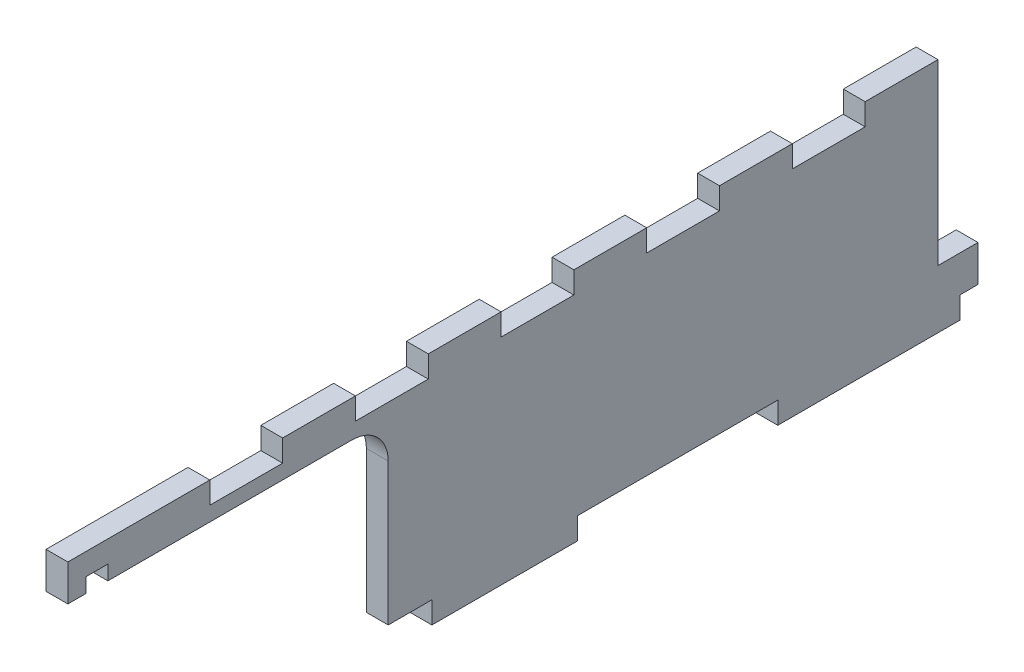
SolidWorks part; units mm, degrees
ref_plane "Front Plane" through (0, 0, 0) normal (0, 0, 1) x (1, 0, 0)
ref_plane "Top Plane" through (0, 0, 0) normal (0, 1, 0) x (1, 0, 0)
ref_plane "Right Plane" through (0, 0, 0) normal (1, 0, 0) x (0, 0, -1)
sketch "Sketch1" plane through (0, 0, 0) normal (1, 0, 0) x (0, 0, -1)
  line L0 (0, 0) -> (250, 0)
  line L1 (250, 0) -> (250, 65)
  line L2 (0, 65) -> (60, 65)
  line L3 (0, 65) -> (0, 0)
  line L4 (60, 65) -> (250, 65)
  point P3 (244, 65)
  point P7 (60, 65)
  point P8 (0, 0)
  point P9 (0, 73.221)
  point P10 (0, 65)
  point P11 (0, 65)
  point P12 (250, 30)
  dimension "D1" = 250
  dimension "D3" = 6
  dimension "D5" = 65
  dimension "D2" = 65
  dimension "D4" = 60
extrude "Boss-Extrude1" add sketch "Sketch1" along normal mid plane 6
sketch "Sketch3" plane through (3, 0, 0) normal (1, 0, 0) x (0, 0, -1)
  line L1 (0, 0) -> (88, 0)
  line L2 (0, 0) -> (0, 55)
  line L3 (0, 55) -> (78, 55)
  line L4 (88, 0) -> (88, 45)
  arc A0 (78, 55) -> (88, 45) centre (78, 45) cw
  dimension "D3" = 10
  dimension "D1" = 88
  dimension "D2" = 55
extrude "Cut-Extrude1" cut sketch "Sketch3" against normal up to surface (6 mm away) up to face at (-3, 32.5, -125)
sketch "Sketch4" plane through (3, 0, 0) normal (1, 0, 0) x (0, 0, -1)
  line L0 (88, 0) -> (250, 0) construction
  line L1 (245, 0) -> (195, 0)
  line L2 (245, 0) -> (245, 6)
  line L3 (250, 65) -> (0, 65) construction
  line L4 (195, 0) -> (195, 6)
  line L5 (250, 0) -> (250, 65) construction
  line L6 (140, 0) -> (100, 0)
  line L7 (140, 0) -> (140, 6)
  line L8 (245, 16) -> (239, 16)
  line L9 (100, 0) -> (100, 6)
  line L10 (140, 6) -> (195, 6)
  line L11 (100, 6) -> (88, 6)
  line L12 (88, 0) -> (88, 45) construction
  line L13 (245, 6) -> (250, 6)
  line L14 (239, 65) -> (250, 65)
  line L15 (78, 55) -> (0, 55) construction
  line L16 (239, 16) -> (239, 65)
  line L17 (245, 16) -> (250, 16)
  line L18 (5, 55) -> (11, 55)
  line L19 (5, 55) -> (5, 59)
  line L20 (250, 16) -> (250, 65)
  line L21 (5, 59) -> (11, 59)
  line L22 (11, 55) -> (11, 59)
  line L23 (250, 65) -> (0, 65) construction
  line M5 (0, 55) -> (78, 55)
  line M7 (88, 45) -> (88, 0)
  line M8 (88, 0) -> (250, 0)
  line M9 (250, 0) -> (250, 65)
  line M10 (250, 65) -> (0, 65)
  dimension "D1" = 6
  dimension "D2" = 5
  dimension "D3" = 50
  dimension "D4" = 55
  dimension "D5" = 40
  dimension "D6" = 6
  dimension "D7" = 10
  dimension "D8" = 5
  dimension "D9" = 6
  dimension "D10" = 6
extrude "Cut-Extrude2" cut sketch "Sketch4" against normal up to surface (6 mm away) contours L9 L11 M7 M8 | L10 L7 L4 M8 | L13 L2 M8 M9 | L8 L17 L16 M9 M10 | L22 L21 L19 M5 up to face at (-3, 41.0102, -108.0102)
sketch "Sketch5" plane through (3, 0, 0) normal (1, 0, 0) x (0, 0, -1)
  line L0 (159, 65) -> (159, 59)
  line L1 (239, 65) -> (0, 65) construction
  line L2 (159, 59) -> (179, 59)
  line L3 (179, 59) -> (179, 65)
  line L4 (179, 65) -> (159, 65)
  line L5 (199, 65) -> (199, 59)
  line L6 (199, 59) -> (219, 59)
  line L7 (219, 59) -> (219, 65)
  line L8 (219, 65) -> (199, 65)
  line L9 (119, 65) -> (119, 59)
  line L10 (119, 59) -> (139, 59)
  line L11 (139, 59) -> (139, 65)
  line L12 (139, 65) -> (119, 65)
  line L13 (79, 65) -> (79, 59)
  line L14 (79, 59) -> (99, 59)
  line L15 (99, 59) -> (99, 65)
  line L16 (99, 65) -> (79, 65)
  line L17 (39, 65) -> (39, 59)
  line L18 (39, 59) -> (59, 59)
  line L19 (59, 59) -> (59, 65)
  line L20 (59, 65) -> (39, 65)
  dimension "D2" = 20
  dimension "D3" = 20
  dimension "D1" = 6
  dimension "D4" = 5
extrude "Cut-Extrude3" cut sketch "Sketch5" against normal up to next
equation "\"Material Thickness\"= 6"
equation "\"D1@Boss-Extrude1\"=\"Material Thickness\""
equation "\"D1@Sketch4\"=\"Material Thickness\""
equation "\"D6@Sketch4\"=\"Material Thickness\""
equation "\"D9@Sketch4\"=\"Material Thickness\""
equation "\"D10@Sketch4\"=\"Material Thickness\""
equation "\"D3@Sketch1\"=\"Material Thickness\""
equation "\"D1@Sketch5\"=\"Material Thickness\""
